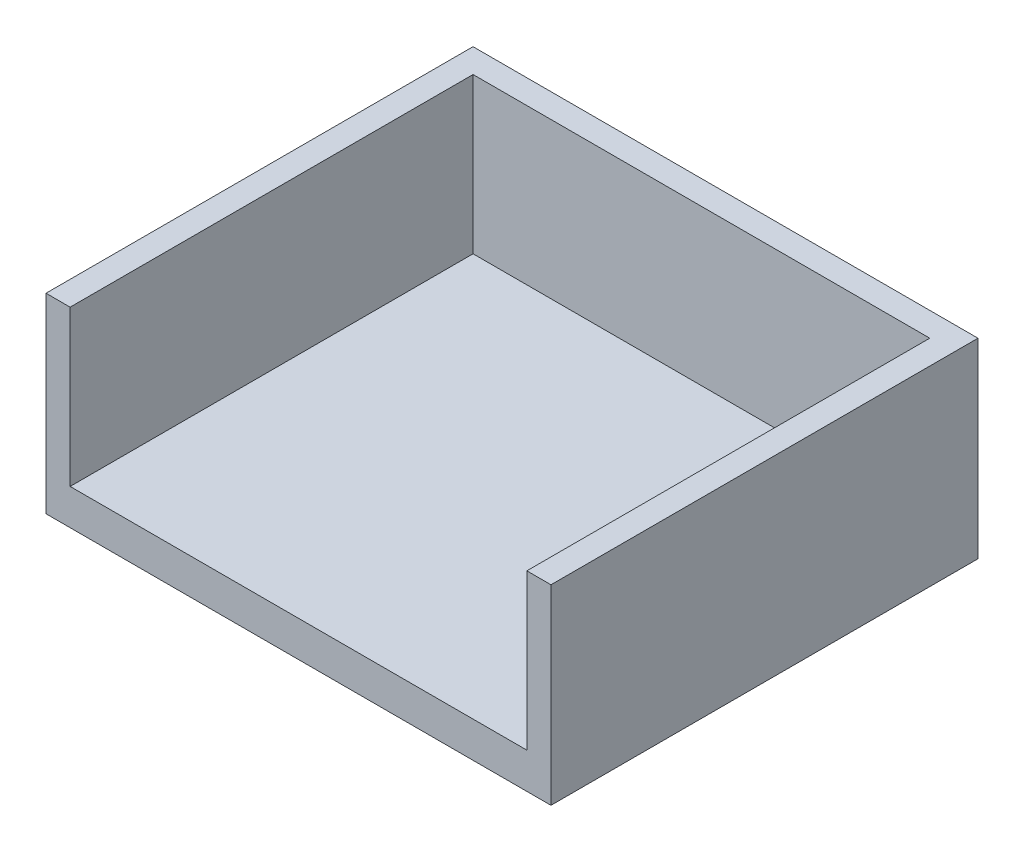
SolidWorks part; units mm, degrees
ref_plane "Front Plane" through (0, 0, 0) normal (0, 0, 1) x (1, 0, 0)
ref_plane "Top Plane" through (0, 0, 0) normal (0, 1, 0) x (1, 0, 0)
ref_plane "Right Plane" through (0, 0, 0) normal (1, 0, 0) x (0, 0, -1)
sketch "Sketch1" plane through (0, 0, 0) normal (0, 1, 0) x (1, 0, 0)
  line L1 (56.505, -47.785) -> (-56.505, -47.785)
  line L2 (56.505, -47.785) -> (56.505, 47.785)
  line L3 (56.505, 47.785) -> (-56.505, 47.785)
  line L4 (-56.505, -47.785) -> (-56.505, 47.785)
  line L5 (56.505, -47.785) -> (-56.505, 47.785) construction
  line L6 (56.505, 47.785) -> (-56.505, -47.785) construction
  point P0 (0, 0)
  dimension "D1" = 113.01
  dimension "D2" = 95.57
extrude "Boss-Extrude1" add sketch "Sketch1" along normal blind 42.75
sketch "Sketch3" plane through (0, 42.75, 0) normal (0, 1, 0) x (1, 0, 0)
  line L0 (-56.505, 47.785) -> (-56.505, -47.785) construction
  line L1 (51.105, -47.7773) -> (-51.105, -47.7773)
  line L2 (51.105, -47.7773) -> (51.105, 42.3927)
  line L3 (51.105, 42.3927) -> (-51.105, 42.3927)
  line L4 (-51.105, -47.7773) -> (-51.105, 42.3927)
  line L5 (51.105, -47.7773) -> (-51.105, 42.3927) construction
  line L6 (51.105, 42.3927) -> (-51.105, -47.7773) construction
  point P0 (0, -2.6923)
  dimension "D1" = 90.17
  dimension "D2" = 102.21
  dimension "D3" = 5.4
extrude "Cut-Extrude1" cut sketch "Sketch3" against normal blind 34.75
sketch "Sketch6" plane through (0, 42.75, 0) normal (0, 1, 0) x (1, 0, 0)
  line L0 (-51.105, -47.7773) -> (51.105, -47.7773) construction
  line L1 (51.105, -52.2515) -> (-51.105, -52.2515)
  line L2 (51.105, -52.2515) -> (51.105, -43.3031)
  line L3 (51.105, -43.3031) -> (-51.105, -43.3031)
  line L4 (-51.105, -52.2515) -> (-51.105, -43.3031)
  line L5 (51.105, -52.2515) -> (-51.105, -43.3031) construction
  line L6 (51.105, -43.3031) -> (-51.105, -52.2515) construction
  point P0 (0, -47.7773)
  dimension "D1" = 102.21
extrude "Cut-Extrude2" cut sketch "Sketch6" against normal blind 34.75
